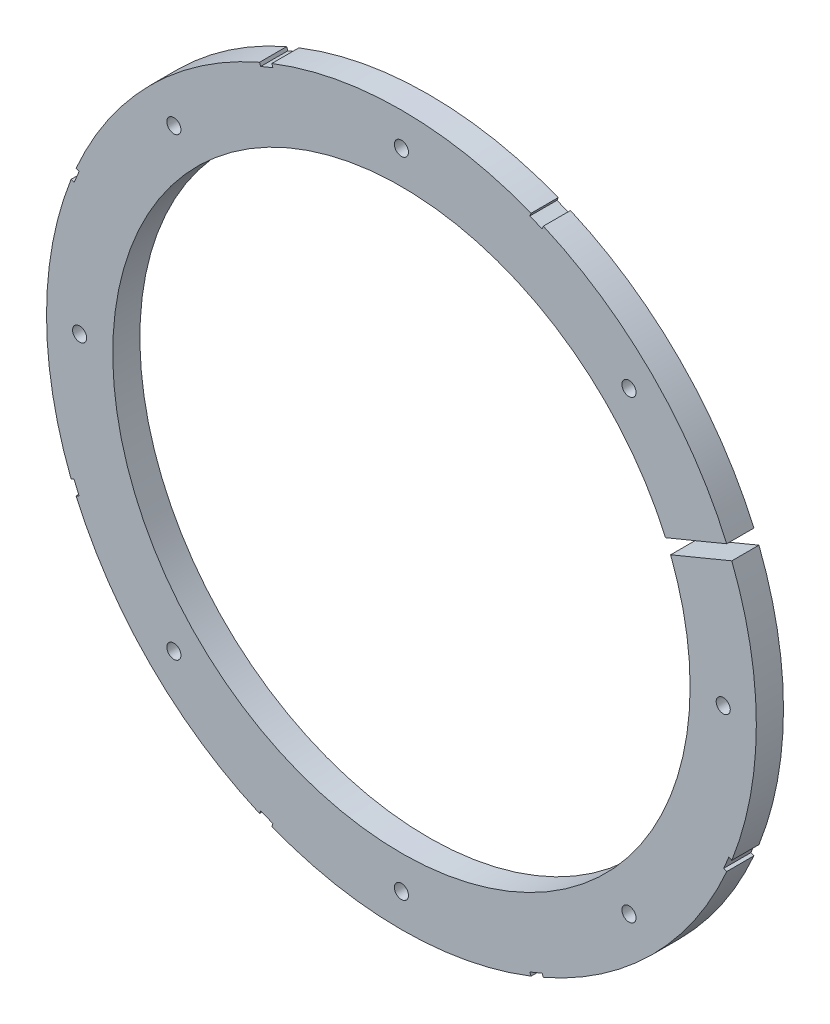
SolidWorks part; units mm, degrees
material "Brass"
ref_plane "Front Plane" through (0, 0, 0) normal (0, 0, 1) x (1, 0, 0)
ref_plane "Top Plane" through (0, 0, 0) normal (0, 1, 0) x (1, 0, 0)
ref_plane "Right Plane" through (0, 0, 0) normal (1, 0, 0) x (0, 0, -1)
sketch "Sketch4" plane through (0, 0, 0) normal (0, 0, 1) x (1, 0, 0)
  circle A0 centre (0, 0) radius 68.072
  dimension "D1" = 136.144
extrude "Boss-Extrude2" add sketch "Sketch4" along normal blind 5.207
sketch "Sketch5" plane through (0, 0, 5.207) normal (0, 0, 1) x (1, 0, 0)
  circle A0 centre (0, 0) radius 55.372
  circle A1 centre (0, 0) radius 68.072 construction
  dimension "D1" = 12.7
extrude "Cut-Extrude5" cut sketch "Sketch5" against normal through all
sketch "Sketch8" plane through (0, 0, 5.207) normal (0, 0, 1) x (1, 0, 0)
  line L0 (68.8576, 29.8964) -> (50.0844, 22.1203)
  line L1 (68.8576, 29.8964) -> (69.8296, 27.5497)
  line L2 (50.0844, 22.1203) -> (51.0564, 19.7736)
  line L3 (69.8296, 27.5497) -> (51.0564, 19.7736)
  line L4 (68.8576, 29.8964) -> (51.0564, 19.7736) construction
  line L5 (50.0844, 22.1203) -> (69.8296, 27.5497) construction
  line L6 (0, 0) -> (50.4438, 0) construction
  line L7 (27.4664, 62.991) -> (25.1197, 63.963)
  line L8 (27.4664, 62.991) -> (26.9803, 61.8177)
  line L9 (25.1197, 63.963) -> (24.6337, 62.7897)
  line L10 (26.9803, 61.8177) -> (24.6337, 62.7897)
  line L11 (25.1197, 63.963) -> (26.9803, 61.8177) construction
  line L12 (27.4664, 62.991) -> (24.6337, 62.7897) construction
  line L13 (-25.1197, 63.963) -> (-27.4664, 62.991)
  line L14 (-25.1197, 63.963) -> (-24.6337, 62.7897)
  line L15 (-24.6337, 62.7897) -> (-26.9803, 61.8177)
  line L16 (-27.4664, 62.991) -> (-26.9803, 61.8177)
  line L17 (-25.1197, 63.963) -> (-26.9803, 61.8177) construction
  line L18 (-27.4664, 62.991) -> (-24.6337, 62.7897) construction
  line L19 (-62.991, 27.4664) -> (-63.963, 25.1197)
  line L20 (-62.991, 27.4664) -> (-61.8177, 26.9803)
  line L21 (-61.8177, 26.9803) -> (-62.7897, 24.6337)
  line L22 (-63.963, 25.1197) -> (-62.7897, 24.6337)
  line L23 (-62.991, 27.4664) -> (-62.7897, 24.6337) construction
  line L24 (-63.963, 25.1197) -> (-61.8177, 26.9803) construction
  line L25 (-63.963, -25.1197) -> (-62.991, -27.4664)
  line L26 (-63.963, -25.1197) -> (-62.7897, -24.6337)
  line L27 (-62.7897, -24.6337) -> (-61.8177, -26.9803)
  line L28 (-62.991, -27.4664) -> (-61.8177, -26.9803)
  line L29 (-63.963, -25.1197) -> (-61.8177, -26.9803) construction
  line L30 (-62.991, -27.4664) -> (-62.7897, -24.6337) construction
  line L31 (-27.4664, -62.991) -> (-25.1197, -63.963)
  line L32 (-27.4664, -62.991) -> (-26.9803, -61.8177)
  line L33 (-26.9803, -61.8177) -> (-24.6337, -62.7897)
  line L34 (-25.1197, -63.963) -> (-24.6337, -62.7897)
  line L35 (-27.4664, -62.991) -> (-24.6337, -62.7897) construction
  line L36 (-25.1197, -63.963) -> (-26.9803, -61.8177) construction
  line L37 (25.1197, -63.963) -> (27.4664, -62.991)
  line L38 (25.1197, -63.963) -> (24.6337, -62.7897)
  line L39 (24.6337, -62.7897) -> (26.9803, -61.8177)
  line L40 (27.4664, -62.991) -> (26.9803, -61.8177)
  line L41 (25.1197, -63.963) -> (26.9803, -61.8177) construction
  line L42 (27.4664, -62.991) -> (24.6337, -62.7897) construction
  line L43 (62.991, -27.4664) -> (63.963, -25.1197)
  line L44 (62.991, -27.4664) -> (61.8177, -26.9803)
  line L45 (61.8177, -26.9803) -> (62.7897, -24.6337)
  line L46 (63.963, -25.1197) -> (62.7897, -24.6337)
  line L47 (62.991, -27.4664) -> (62.7897, -24.6337) construction
  line L48 (63.963, -25.1197) -> (61.8177, -26.9803) construction
  circle A0 centre (0, 0) radius 55.372 construction
  circle A1 centre (0, 0) radius 68.072 construction
  point P1 (59.957, 24.835)
  point P3 (26.05, 62.8903)
  point P11 (-26.05, 62.8903)
  point P20 (-62.8903, 26.05)
  point P25 (-62.8903, -26.05)
  point P26 (0, 0)
  point P31 (-26.05, -62.8903)
  point P36 (26.05, -62.8903)
  point P41 (62.8903, -26.05)
  point P46 (0, 0)
  dimension "D1" = 20.32
  dimension "D2" = 9.525
  dimension "D3" = 2.54
  dimension "D4" = 22.5
  dimension "D5" = 1.27
  dimension "D6" = 2.54
  dimension "D7" = 1.27
  dimension "D8" = 1.27
  dimension "D9" = 0.635
  dimension "D10" = 67.5
  dimension "D12" = 0.635
  dimension "D13" = 22.5
  dimension "D11" = 7
extrude "Cut-Extrude11" cut sketch "Sketch8" against normal through all
hole_wizard "#6-32 Tapped Hole1" positions "Sketch10" profile "Sketch9" tap size "#6-32" standard "ANSI Inch" end condition through all
sketch "Sketch10" plane through (0, 0, 5.207) normal (0, 0, 1) x (1, 0, 0)
  line L7 (0, 0) -> (43.644, 43.644) construction
  line L9 (0, 0) -> (61.722, 0) construction
  line L11 (0, 0) -> (43.644, -43.644) construction
  arc A0 (50.6576, 22.3577) -> (51.6296, 20.011) centre (0, 0) ccw construction
  point P0 (61.722, 0)
  point P27 (43.644, -43.644)
  point P28 (0, -61.722)
  point P29 (-43.644, -43.644)
  point P30 (-61.722, 0)
  point P31 (-43.644, 43.644)
  point P32 (0, 61.722)
  point P33 (43.644, 43.644)
  dimension "D1" = 6.35
  dimension "D2" = 45
  dimension "D3" = 45
  dimension "D5" = 6.35
  dimension "D4" = 8
cosmetic thread "Hole Thread1" parameters "D2"=3.5052
cosmetic thread "Hole Thread2" parameters "D2"=3.5052
cosmetic thread "Hole Thread3" parameters "D2"=3.5052
cosmetic thread "Hole Thread4" parameters "D2"=3.5052
cosmetic thread "Hole Thread5" parameters "D2"=3.5052
cosmetic thread "Hole Thread6" parameters "D2"=3.5052
cosmetic thread "Hole Thread7" parameters "D2"=3.5052
cosmetic thread "Hole Thread8" parameters "D2"=3.5052
sketch "Sketch9" plane through (61.722, 0, 5.207) normal (1, 0, 0) x (0, -1, 0)
  line L0 (0, 0) -> (0, 5.207)
  line L1 (0, 5.207) -> (1.3525, 5.207)
  line L2 (1.3525, 5.207) -> (1.3525, 0)
  line L5 (1.3525, 0) -> (0, 0)
  line L11 (0, -6.35) -> (0, 107.95) construction
  dimension "Thru Tap Drill Dia." = 2.7051
  dimension "Thru Tap Drill Depth" = 5.207
